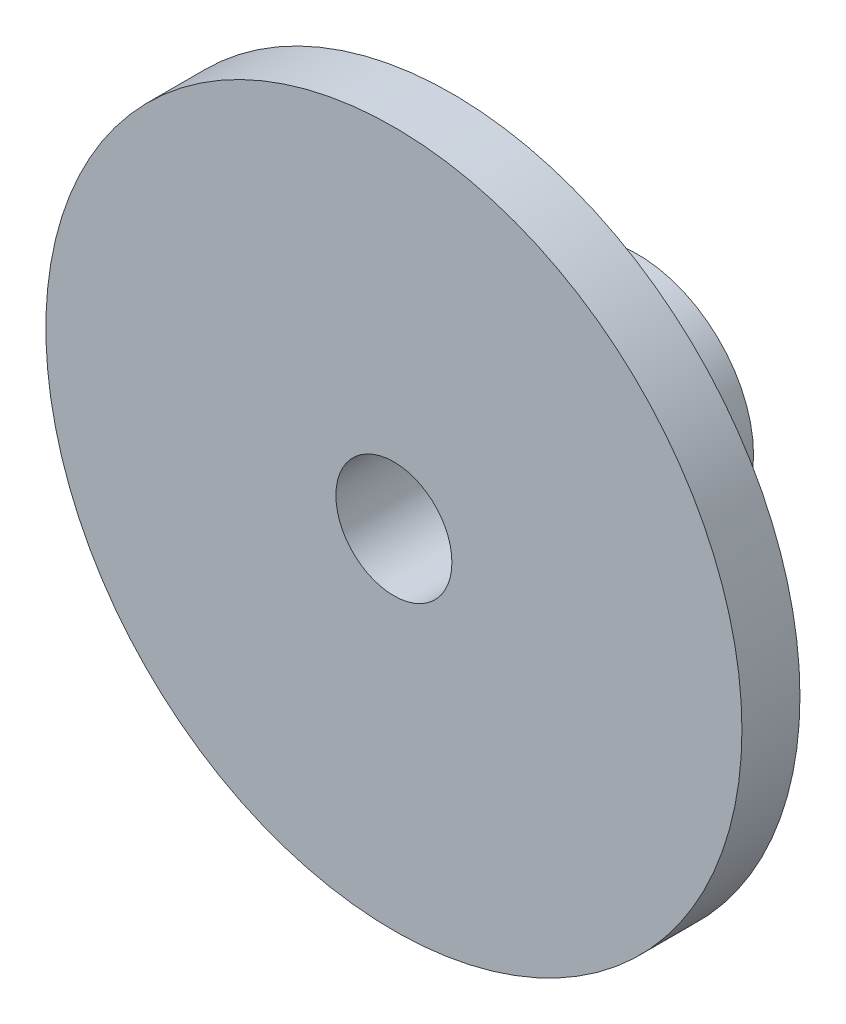
SolidWorks part; units mm, degrees
material "6061-T6 (SS)"
ref_plane "Front Plane" through (0, 0, 0) normal (0, 0, 1) x (1, 0, 0)
ref_plane "Top Plane" through (0, 0, 0) normal (0, 1, 0) x (1, 0, 0)
ref_plane "Right Plane" through (0, 0, 0) normal (1, 0, 0) x (0, 0, -1)
sketch "Sketch1" plane through (0, 0, 0) normal (0, 0, 1) x (1, 0, 0)
  circle A0 centre (0, 0) radius 3.175
  circle A1 centre (0, 0) radius 19.05
  dimension "D1" = 6.35
  dimension "D2" = 38.1
extrude "Boss-Extrude1" add sketch "Sketch1" along normal blind 3.175
sketch "Sketch2" plane through (0, 0, 0) normal (0, 0, -1) x (-1, 0, 0)
  circle A0 centre (0, 0) radius 3.175 construction
  circle A1 centre (0, 0) radius 3.175
  circle A2 centre (0, 0) radius 6.35
  dimension "D1" = 3.175
extrude "Boss-Extrude2" add sketch "Sketch2" along normal blind 10.16
